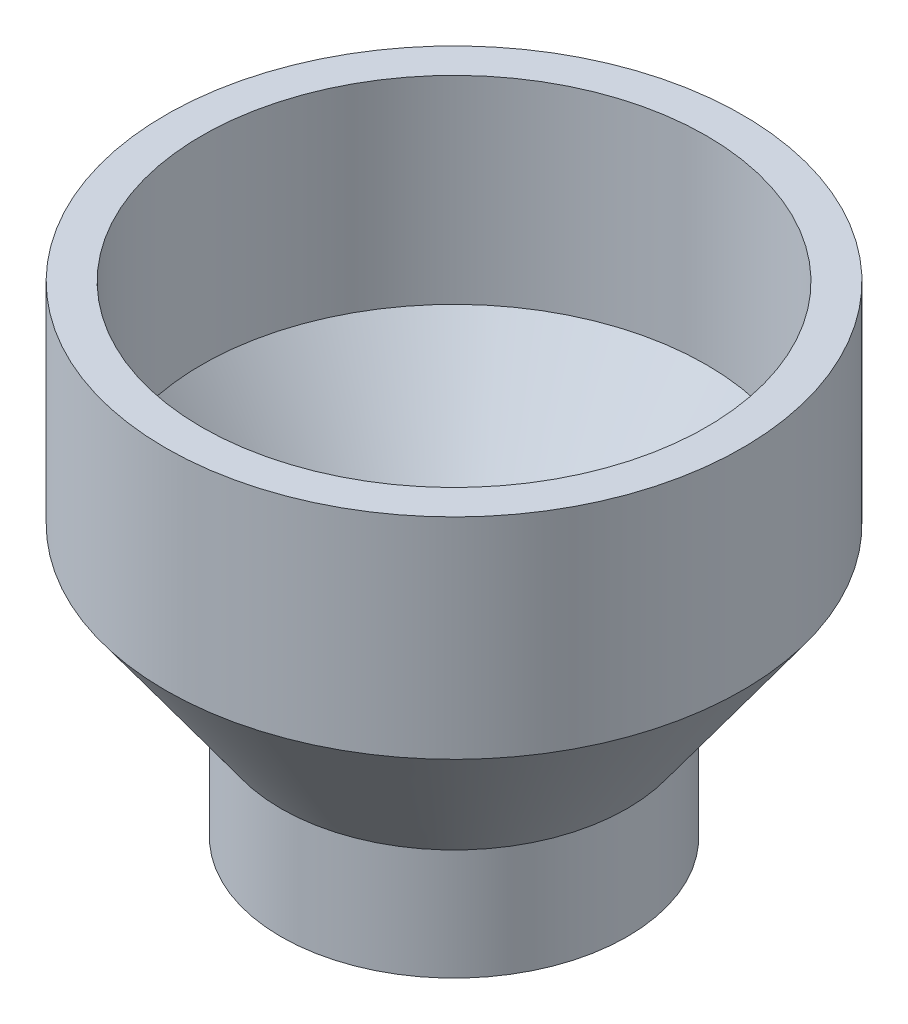
SolidWorks part; units mm, degrees
ref_plane "Front" through (0, 0, 0) normal (0, 0, 1) x (1, 0, 0)
ref_plane "Top" through (0, 0, 0) normal (0, 1, 0) x (1, 0, 0)
ref_plane "Right" through (0, 0, 0) normal (1, 0, 0) x (0, 0, -1)
sketch "Sketch1" plane through (0, 0, 0) normal (0, 0, 1) x (1, 0, 0)
  line L0 (-24.13, 0) -> (-24.13, 21.59)
  line L1 (-24.13, 21.59) -> (-44.45, 49.784)
  line L2 (-44.45, 49.784) -> (-44.45, 84.709)
  line L3 (0, 0) -> (0, -10.4431) construction
  point P7 (0, 0)
  dimension "D1" = 88.9
  dimension "D2" = 48.26
  dimension "D3" = 84.709
  dimension "D4" = 34.925
  dimension "D5" = 21.59
revolve "Revolve-Thin1" add sketch "Sketch1" angle 360 about L3 wall 6.35
